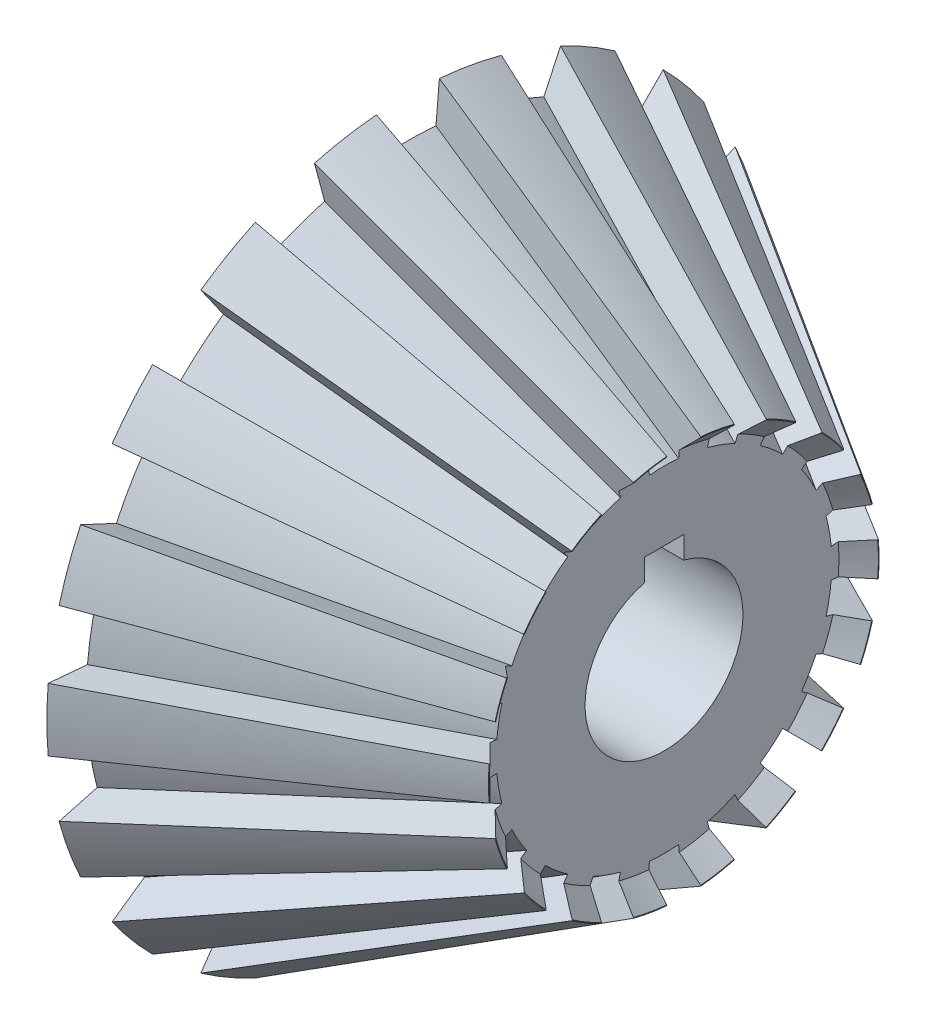
SolidWorks part; units mm, degrees
ref_plane "Plano frontal" through (0, 0, 0) normal (0, 0, 1) x (1, 0, 0)
ref_plane "Plano superior" through (0, 0, 0) normal (0, 1, 0) x (1, 0, 0)
ref_plane "Plano direito" through (0, 0, 0) normal (1, 0, 0) x (0, 0, -1)
sketch "Esboço1" plane through (0, 0, 0) normal (0, 0, 1) x (1, 0, 0)
  line L0 (0, 20) -> (0, 39.6875)
  line L1 (0, 39.6875) -> (26.1937, 39.6875)
  line L2 (26.1937, 39.6875) -> (26.1938, 91.44)
  line L3 (26.1938, 91.44) -> (96.0438, 49.4699)
  line L5 (206.3616, 0) -> (0, 0) construction
  line L6 (0, 20) -> (96.0437, 20)
  line L7 (96.0438, 49.4699) -> (96.0437, 20)
  dimension "D1" = 79.375
  dimension "D2" = 40
  dimension "D3" = 26.1937
  dimension "D4" = 182.88
  dimension "D5" = 31
  dimension "D6" = 69.85
revolve "Revolução1" add sketch "Esboço1" angle 360 about L5
chamfer "Chanfro1" distance 3.9688 angle 45 1 edges at (0, 39.6875, 0)
sketch "Esboço3" plane through (0, 0, 0) normal (0, 0, 1) x (1, 0, 0)
  line L0 (96.0437, 0) -> (96.0438, 49.4699) construction
  line L1 (96.0438, -49.4699) -> (96.0438, 49.4699) construction
  line L2 (96.0438, 49.4699) -> (26.1938, 91.44)
  line L3 (96.0437, 0) -> (172.3635, 0) construction
  line L4 (96.0437, 39.4858) -> (26.1938, 81.4559)
  line L5 (26.1938, 91.44) -> (26.1938, 81.4559)
  line L7 (96.0438, 49.4699) -> (96.0437, 39.4858)
  dimension "D1" = 31
revolve "Corte-Revolução1" cut sketch "Esboço3" angle 10 mid plane about L3
pattern_circular "PadrãoCircular1" count 18 over 360 about axis through (0, 0, 0) along (1, 0, 0) of "Corte-Revolução1"
sketch "Esboço7" plane through (0, 0, 0) normal (0, 1, 0) x (1, 0, 0)
  line L0 (91.0437, 0) -> (96.0437, 0) construction
  line L1 (96.0437, -3.4414) -> (96.0437, 3.4414) construction
  line L2 (96.0437, 0) -> (96.0438, 49.2816)
  line L3 (96.0438, 49.2816) -> (91.0437, 44.2816)
  line L4 (91.0437, 44.2816) -> (91.0437, 0)
  line L5 (96.0437, 0) -> (91.0437, 0)
  dimension "D1" = 45
  dimension "D2" = 5
revolve "Corte-Revolução2" cut sketch "Esboço7" angle 360 about L0
sketch "Esboço8" plane through (91.0437, 0, 0) normal (1, 0, 0) x (0, 0, -1)
  line L1 (5, 15) -> (-5, 15)
  line L2 (5, 15) -> (5, 25)
  line L3 (5, 25) -> (-5, 25)
  line L4 (-5, 15) -> (-5, 25)
  line L5 (5, 15) -> (-5, 25) construction
  line L6 (5, 25) -> (-5, 15) construction
  circle A0 centre (0, 0) radius 20 construction
  point P0 (0, 20)
  dimension "D1" = 5
  dimension "D2" = 10
extrude "Corte-extrusão1" cut sketch "Esboço8" against normal through all
